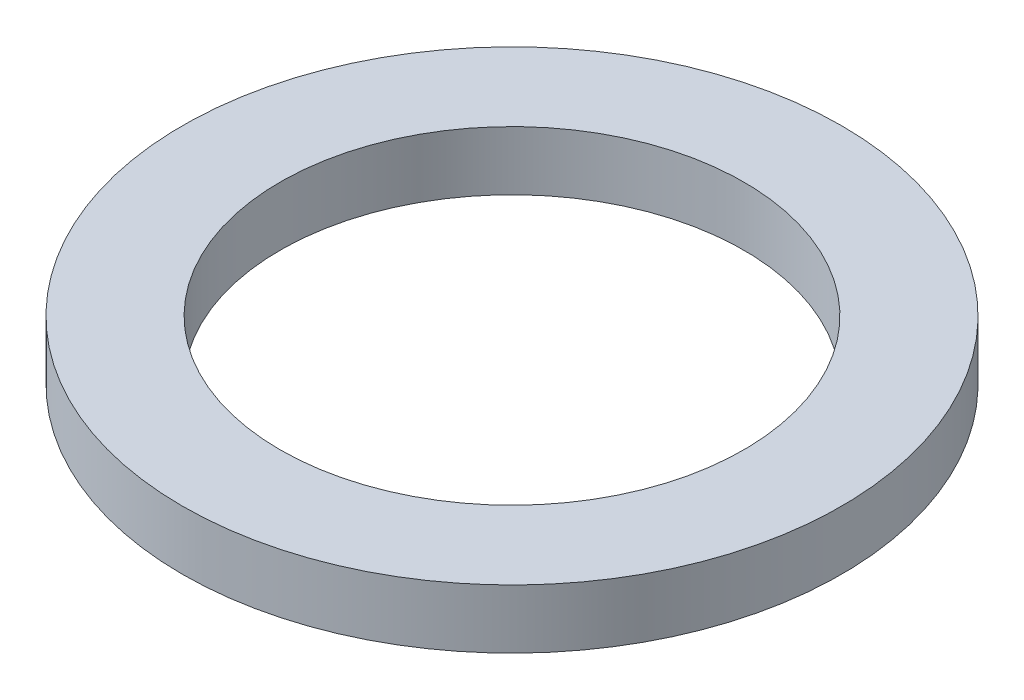
SolidWorks part; units mm, degrees
ref_plane "Front Plane" through (0, 0, 0) normal (0, 0, 1) x (1, 0, 0)
ref_plane "Top Plane" through (0, 0, 0) normal (0, 1, 0) x (1, 0, 0)
ref_plane "Right Plane" through (0, 0, 0) normal (1, 0, 0) x (0, 0, -1)
sketch "Sketch1" plane through (0, 0, 0) normal (0, 1, 0) x (1, 0, 0)
  circle A0 centre (0, 0) radius 11.1633
  circle A1 centre (0, 0) radius 7.855
  dimension "D1" = 22.3266
  dimension "D2" = 15.7099
extrude "Boss-Extrude1" add sketch "Sketch1" along normal blind 2
